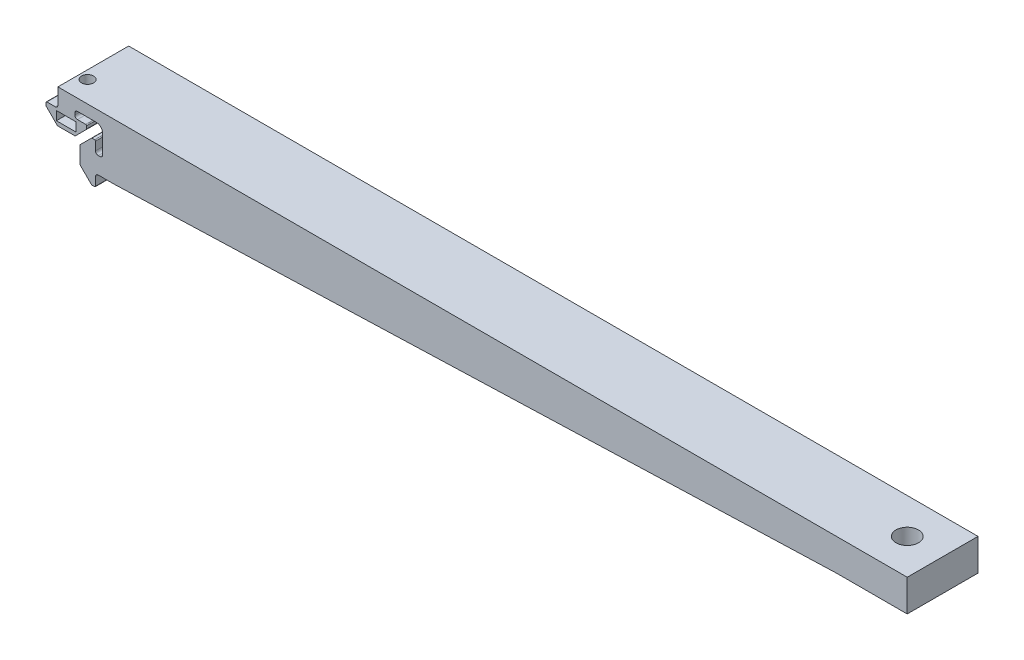
SolidWorks part; units mm, degrees
ref_plane "Front Plane" through (0, 0, 0) normal (0, 0, 1) x (1, 0, 0)
ref_plane "Top Plane" through (0, 0, 0) normal (0, 1, 0) x (1, 0, 0)
ref_plane "Right Plane" through (0, 0, 0) normal (1, 0, 0) x (0, 0, -1)
sketch "Sketch1" plane through (0, 0, 0) normal (0, 0, 1) x (1, 0, 0)
  line L0 (-3.138, 10.25) -> (-8.5, 10.25) construction
  line L1 (-10.25, 8.5) -> (-10.25, 3.138) construction
  line L2 (-9.492, 2.38) -> (-9.008, 2.38) construction
  line L3 (-8.25, 3.138) -> (-8.25, 5.487) construction
  line L4 (-7.992, 5.745) -> (-7.2662, 5.745) construction
  line L5 (-7.0838, 5.6694) -> (-3.9806, 2.5662) construction
  line L6 (-3.905, 2.3838) -> (-3.905, -2.3841) construction
  line L7 (-3.9806, -2.5665) -> (-7.0835, -5.6694) construction
  line L8 (-7.2659, -5.745) -> (-7.992, -5.745) construction
  line L9 (-8.25, -5.487) -> (-8.25, -3.138) construction
  line L10 (-9.008, -2.38) -> (-9.492, -2.38) construction
  line L11 (-10.25, -3.138) -> (-10.25, -8.5) construction
  line L12 (-8.5, -10.25) -> (-3.138, -10.25) construction
  line L13 (-2.38, -9.492) -> (-2.38, -9.008) construction
  line L14 (-3.138, -8.25) -> (-5.487, -8.25) construction
  line L15 (-5.745, -7.992) -> (-5.745, -7.2662) construction
  line L16 (-5.6694, -7.0838) -> (-2.5662, -3.9806) construction
  line L17 (-2.3838, -3.905) -> (2.3841, -3.905) construction
  line L18 (2.5665, -3.9806) -> (5.6694, -7.0835) construction
  line L19 (5.745, -7.2659) -> (5.745, -7.992) construction
  line L20 (5.487, -8.25) -> (3.138, -8.25) construction
  line L21 (2.38, -9.008) -> (2.38, -9.492) construction
  line L22 (3.138, -10.25) -> (8.5, -10.25) construction
  line L23 (10.25, -8.5) -> (10.25, -3.138) construction
  line L24 (9.492, -2.38) -> (9.008, -2.38)
  line L25 (8.25, -3.138) -> (8.25, -5.487)
  line L26 (7.992, -5.745) -> (7.2662, -5.745)
  line L27 (7.0838, -5.6694) -> (3.9806, -2.5662)
  line L28 (3.905, -2.3838) -> (3.905, 2.3841)
  line L29 (3.9806, 2.5665) -> (7.0835, 5.6694)
  line L30 (7.2659, 5.745) -> (7.992, 5.745)
  line L31 (8.25, 5.487) -> (8.25, 3.138)
  line L32 (9.008, 2.38) -> (9.492, 2.38)
  line L33 (10.25, 3.138) -> (10.25, 8.5)
  line L34 (8.5, 10.25) -> (3.138, 10.25)
  line L35 (2.38, 9.492) -> (2.38, 9.008)
  line L36 (3.138, 8.25) -> (5.487, 8.25)
  line L37 (5.745, 7.992) -> (5.745, 7.2662)
  line L38 (5.6694, 7.0838) -> (2.5662, 3.9806)
  line L39 (2.3838, 3.905) -> (-2.3841, 3.905)
  line L40 (-2.5665, 3.9806) -> (-5.6694, 7.0835)
  line L41 (-5.745, 7.2659) -> (-5.745, 7.992)
  line L42 (-5.487, 8.25) -> (-3.138, 8.25)
  line L43 (-2.38, 9.008) -> (-2.38, 9.492)
  line L44 (-10, -3.138) -> (-10, -8.5)
  line L45 (-8.5, -10) -> (-3.138, -10)
  line L46 (-2.63, -9.492) -> (-2.63, -9.008)
  line L47 (-3.138, -8.5) -> (-5.487, -8.5)
  line L48 (-5.995, -7.992) -> (-5.995, -7.2662)
  line L49 (-5.8462, -6.907) -> (-2.743, -3.8038)
  line L50 (-2.3838, -3.655) -> (2.3841, -3.655)
  line L51 (2.7433, -3.8038) -> (5.8462, -6.9067)
  line L52 (5.995, -7.2659) -> (5.995, -7.992)
  line L53 (5.487, -8.5) -> (3.138, -8.5)
  line L54 (2.63, -9.008) -> (2.63, -9.492)
  line L55 (3.138, -10) -> (8.5, -10)
  line L56 (10, -8.5) -> (10, -3.138)
  line L57 (9.492, -2.63) -> (9.008, -2.63)
  line L58 (8.5, -3.138) -> (8.5, -5.487)
  line L59 (7.992, -5.995) -> (7.2662, -5.995)
  line L60 (6.907, -5.8462) -> (3.8038, -2.743)
  line L61 (3.655, -2.3838) -> (3.655, 2.3841)
  line L62 (3.8038, 2.7433) -> (6.9067, 5.8462)
  line L63 (7.2659, 5.995) -> (7.992, 5.995)
  line L64 (8.5, 5.487) -> (8.5, 3.138)
  line L65 (9.008, 2.63) -> (9.492, 2.63)
  line L66 (10, 3.138) -> (10, 8.5)
  line L67 (8.5, 10) -> (3.138, 10)
  line L68 (2.63, 9.492) -> (2.63, 9.008)
  line L69 (3.138, 8.5) -> (5.487, 8.5)
  line L70 (5.995, 7.992) -> (5.995, 7.2662)
  line L71 (5.8462, 6.907) -> (2.743, 3.8038)
  line L72 (2.3838, 3.655) -> (-2.3841, 3.655)
  line L73 (-2.7433, 3.8038) -> (-5.8462, 6.9067)
  line L74 (-5.995, 7.2659) -> (-5.995, 7.992)
  line L75 (-5.487, 8.5) -> (-3.138, 8.5)
  line L76 (-2.63, 9.008) -> (-2.63, 9.492)
  line L77 (-3.138, 10) -> (-8.5, 10)
  line L78 (-10, 8.5) -> (-10, 3.138)
  line L79 (-9.492, 2.63) -> (-9.008, 2.63)
  line L80 (-8.5, 3.138) -> (-8.5, 5.487)
  line L81 (-7.992, 5.995) -> (-7.2662, 5.995)
  line L82 (-6.907, 5.8462) -> (-3.8038, 2.743)
  line L83 (-3.655, 2.3838) -> (-3.655, -2.3841)
  line L84 (-3.8038, -2.7433) -> (-6.9067, -5.8462)
  line L85 (-7.2659, -5.995) -> (-7.992, -5.995)
  line L86 (-8.5, -5.487) -> (-8.5, -3.138)
  line L87 (-9.008, -2.63) -> (-9.492, -2.63)
  line L88 (-10, -3.138) -> (-10, -8.5) construction
  line L89 (-8.5, -10) -> (-3.138, -10) construction
  line L90 (-2.63, -9.492) -> (-2.63, -9.008) construction
  line L91 (-3.138, -8.5) -> (-5.487, -8.5) construction
  line L92 (-5.995, -7.992) -> (-5.995, -7.2662) construction
  line L93 (-5.8462, -6.907) -> (-2.743, -3.8038) construction
  line L94 (-2.3838, -3.655) -> (2.3841, -3.655) construction
  line L95 (2.7433, -3.8038) -> (5.8462, -6.9067) construction
  line L96 (5.995, -7.2659) -> (5.995, -7.992) construction
  line L97 (5.487, -8.5) -> (3.138, -8.5) construction
  line L98 (2.63, -9.008) -> (2.63, -9.492) construction
  line L99 (3.138, -10) -> (8.5, -10) construction
  line L100 (10, -8.5) -> (10, -3.138) construction
  line L101 (9.492, -2.63) -> (9.008, -2.63) construction
  line L102 (8.5, -3.138) -> (8.5, -5.487) construction
  line L103 (7.992, -5.995) -> (7.2662, -5.995) construction
  line L104 (6.907, -5.8462) -> (3.8038, -2.743) construction
  line L105 (3.655, -2.3838) -> (3.655, 2.3841) construction
  line L106 (3.8038, 2.7433) -> (6.9067, 5.8462) construction
  line L107 (7.2659, 5.995) -> (7.992, 5.995) construction
  line L108 (8.5, 5.487) -> (8.5, 3.138) construction
  line L109 (9.008, 2.63) -> (9.492, 2.63) construction
  line L110 (10, 3.138) -> (10, 8.5) construction
  line L111 (8.5, 10) -> (3.138, 10) construction
  line L112 (2.63, 9.492) -> (2.63, 9.008) construction
  line L113 (3.138, 8.5) -> (5.487, 8.5) construction
  line L114 (5.995, 7.992) -> (5.995, 7.2662) construction
  line L115 (5.8462, 6.907) -> (2.743, 3.8038) construction
  line L116 (2.3838, 3.655) -> (-2.3841, 3.655) construction
  line L117 (-2.7433, 3.8038) -> (-5.8462, 6.9067) construction
  line L118 (-5.995, 7.2659) -> (-5.995, 7.992) construction
  line L119 (-5.487, 8.5) -> (-3.138, 8.5) construction
  line L120 (-2.63, 9.008) -> (-2.63, 9.492) construction
  line L121 (-3.138, 10) -> (-8.5, 10) construction
  line L122 (-10, 8.5) -> (-10, 3.138) construction
  line L123 (-9.492, 2.63) -> (-9.008, 2.63) construction
  line L124 (-8.5, 3.138) -> (-8.5, 5.487) construction
  line L125 (-7.992, 5.995) -> (-7.2662, 5.995) construction
  line L126 (-6.907, 5.8462) -> (-3.8038, 2.743) construction
  line L127 (-3.655, 2.3838) -> (-3.655, -2.3841) construction
  line L128 (-3.8038, -2.7433) -> (-6.9067, -5.8462) construction
  line L129 (-7.2659, -5.995) -> (-7.992, -5.995) construction
  line L130 (-8.5, -5.487) -> (-8.5, -3.138) construction
  line L131 (-9.008, -2.63) -> (-9.492, -2.63) construction
  line L132 (-2.38, 9.492) -> (-2.38, 13.492)
  line L133 (-2.38, 13.492) -> (13.492, 13.492)
  line L134 (13.492, 13.492) -> (13.492, -2.38)
  line L135 (13.492, -2.38) -> (9.492, -2.38)
  arc A0 (-8.5, 10.25) -> (-10.25, 8.5) centre (-8.5, 8.5) ccw construction
  arc A1 (-10.25, 3.138) -> (-9.492, 2.38) centre (-9.492, 3.138) ccw construction
  arc A2 (-9.008, 2.38) -> (-8.25, 3.138) centre (-9.008, 3.138) ccw construction
  arc A3 (-7.992, 5.745) -> (-8.25, 5.487) centre (-7.992, 5.487) ccw construction
  arc A4 (-7.0838, 5.6694) -> (-7.2662, 5.745) centre (-7.2662, 5.487) ccw
  arc A5 (-3.905, 2.3838) -> (-3.9806, 2.5662) centre (-4.163, 2.3838) ccw construction
  arc A6 (-3.9806, -2.5665) -> (-3.905, -2.3841) centre (-4.163, -2.3841) ccw construction
  arc A7 (-7.2659, -5.745) -> (-7.0835, -5.6694) centre (-7.2659, -5.487) ccw construction
  arc A8 (-8.25, -5.487) -> (-7.992, -5.745) centre (-7.992, -5.487) ccw construction
  arc A9 (-8.25, -3.138) -> (-9.008, -2.38) centre (-9.008, -3.138) ccw construction
  arc A10 (-9.492, -2.38) -> (-10.25, -3.138) centre (-9.492, -3.138) ccw construction
  arc A11 (-10.25, -8.5) -> (-8.5, -10.25) centre (-8.5, -8.5) ccw construction
  arc A12 (-3.138, -10.25) -> (-2.38, -9.492) centre (-3.138, -9.492) ccw construction
  arc A13 (-2.38, -9.008) -> (-3.138, -8.25) centre (-3.138, -9.008) ccw construction
  arc A14 (-5.745, -7.992) -> (-5.487, -8.25) centre (-5.487, -7.992) ccw
  arc A15 (-5.6694, -7.0838) -> (-5.745, -7.2662) centre (-5.487, -7.2662) ccw construction
  arc A16 (-2.3838, -3.905) -> (-2.5662, -3.9806) centre (-2.3838, -4.163) ccw construction
  arc A17 (2.5665, -3.9806) -> (2.3841, -3.905) centre (2.3841, -4.163) ccw construction
  arc A18 (5.745, -7.2659) -> (5.6694, -7.0835) centre (5.487, -7.2659) ccw construction
  arc A19 (5.487, -8.25) -> (5.745, -7.992) centre (5.487, -7.992) ccw
  arc A20 (3.138, -8.25) -> (2.38, -9.008) centre (3.138, -9.008) ccw construction
  arc A21 (2.38, -9.492) -> (3.138, -10.25) centre (3.138, -9.492) ccw construction
  arc A22 (8.5, -10.25) -> (10.25, -8.5) centre (8.5, -8.5) ccw construction
  arc A23 (10.25, -3.138) -> (9.492, -2.38) centre (9.492, -3.138) ccw construction
  arc A24 (9.008, -2.38) -> (8.25, -3.138) centre (9.008, -3.138) ccw
  arc A25 (7.992, -5.745) -> (8.25, -5.487) centre (7.992, -5.487) ccw
  arc A26 (7.0838, -5.6694) -> (7.2662, -5.745) centre (7.2662, -5.487) ccw
  arc A27 (3.905, -2.3838) -> (3.9806, -2.5662) centre (4.163, -2.3838) ccw
  arc A28 (3.9806, 2.5665) -> (3.905, 2.3841) centre (4.163, 2.3841) ccw
  arc A29 (7.2659, 5.745) -> (7.0835, 5.6694) centre (7.2659, 5.487) ccw
  arc A30 (8.25, 5.487) -> (7.992, 5.745) centre (7.992, 5.487) ccw
  arc A31 (8.25, 3.138) -> (9.008, 2.38) centre (9.008, 3.138) ccw
  arc A32 (9.492, 2.38) -> (10.25, 3.138) centre (9.492, 3.138) ccw
  arc A33 (10.25, 8.5) -> (8.5, 10.25) centre (8.5, 8.5) ccw
  arc A34 (3.138, 10.25) -> (2.38, 9.492) centre (3.138, 9.492) ccw
  arc A35 (2.38, 9.008) -> (3.138, 8.25) centre (3.138, 9.008) ccw
  arc A36 (5.745, 7.992) -> (5.487, 8.25) centre (5.487, 7.992) ccw
  arc A37 (5.6694, 7.0838) -> (5.745, 7.2662) centre (5.487, 7.2662) ccw
  arc A38 (2.3838, 3.905) -> (2.5662, 3.9806) centre (2.3838, 4.163) ccw
  arc A39 (-2.5665, 3.9806) -> (-2.3841, 3.905) centre (-2.3841, 4.163) ccw
  arc A40 (-5.745, 7.2659) -> (-5.6694, 7.0835) centre (-5.487, 7.2659) ccw
  arc A41 (-5.487, 8.25) -> (-5.745, 7.992) centre (-5.487, 7.992) ccw
  arc A42 (-3.138, 8.25) -> (-2.38, 9.008) centre (-3.138, 9.008) ccw
  arc A43 (-2.38, 9.492) -> (-3.138, 10.25) centre (-3.138, 9.492) ccw construction
  arc A44 (-10, -8.5) -> (-8.5, -10) centre (-8.5, -8.5) ccw
  arc A45 (-3.138, -10) -> (-2.63, -9.492) centre (-3.138, -9.492) ccw
  arc A46 (-2.63, -9.008) -> (-3.138, -8.5) centre (-3.138, -9.008) ccw
  arc A47 (-5.995, -7.992) -> (-5.487, -8.5) centre (-5.487, -7.992) ccw
  arc A48 (-5.8462, -6.907) -> (-5.995, -7.2662) centre (-5.487, -7.2662) ccw
  arc A49 (-2.3838, -3.655) -> (-2.743, -3.8038) centre (-2.3838, -4.163) ccw
  arc A50 (2.7433, -3.8038) -> (2.3841, -3.655) centre (2.3841, -4.163) ccw
  arc A51 (5.995, -7.2659) -> (5.8462, -6.9067) centre (5.487, -7.2659) ccw
  arc A52 (5.487, -8.5) -> (5.995, -7.992) centre (5.487, -7.992) ccw
  arc A53 (3.138, -8.5) -> (2.63, -9.008) centre (3.138, -9.008) ccw
  arc A54 (2.63, -9.492) -> (3.138, -10) centre (3.138, -9.492) ccw
  arc A55 (8.5, -10) -> (10, -8.5) centre (8.5, -8.5) ccw
  arc A56 (10, -3.138) -> (9.492, -2.63) centre (9.492, -3.138) ccw
  arc A57 (9.008, -2.63) -> (8.5, -3.138) centre (9.008, -3.138) ccw
  arc A58 (7.992, -5.995) -> (8.5, -5.487) centre (7.992, -5.487) ccw
  arc A59 (6.907, -5.8462) -> (7.2662, -5.995) centre (7.2662, -5.487) ccw
  arc A60 (3.655, -2.3838) -> (3.8038, -2.743) centre (4.163, -2.3838) ccw
  arc A61 (3.8038, 2.7433) -> (3.655, 2.3841) centre (4.163, 2.3841) ccw
  arc A62 (7.2659, 5.995) -> (6.9067, 5.8462) centre (7.2659, 5.487) ccw
  arc A63 (8.5, 5.487) -> (7.992, 5.995) centre (7.992, 5.487) ccw
  arc A64 (8.5, 3.138) -> (9.008, 2.63) centre (9.008, 3.138) ccw
  arc A65 (9.492, 2.63) -> (10, 3.138) centre (9.492, 3.138) ccw
  arc A66 (10, 8.5) -> (8.5, 10) centre (8.5, 8.5) ccw
  arc A67 (3.138, 10) -> (2.63, 9.492) centre (3.138, 9.492) ccw
  arc A68 (2.63, 9.008) -> (3.138, 8.5) centre (3.138, 9.008) ccw
  arc A69 (5.995, 7.992) -> (5.487, 8.5) centre (5.487, 7.992) ccw
  arc A70 (5.8462, 6.907) -> (5.995, 7.2662) centre (5.487, 7.2662) ccw
  arc A71 (2.3838, 3.655) -> (2.743, 3.8038) centre (2.3838, 4.163) ccw
  arc A72 (-2.7433, 3.8038) -> (-2.3841, 3.655) centre (-2.3841, 4.163) ccw
  arc A73 (-5.995, 7.2659) -> (-5.8462, 6.9067) centre (-5.487, 7.2659) ccw
  arc A74 (-5.487, 8.5) -> (-5.995, 7.992) centre (-5.487, 7.992) ccw
  arc A75 (-3.138, 8.5) -> (-2.63, 9.008) centre (-3.138, 9.008) ccw
  arc A76 (-2.63, 9.492) -> (-3.138, 10) centre (-3.138, 9.492) ccw
  arc A77 (-8.5, 10) -> (-10, 8.5) centre (-8.5, 8.5) ccw
  arc A78 (-10, 3.138) -> (-9.492, 2.63) centre (-9.492, 3.138) ccw
  arc A79 (-9.008, 2.63) -> (-8.5, 3.138) centre (-9.008, 3.138) ccw
  arc A80 (-7.992, 5.995) -> (-8.5, 5.487) centre (-7.992, 5.487) ccw
  arc A81 (-6.907, 5.8462) -> (-7.2662, 5.995) centre (-7.2662, 5.487) ccw
  arc A82 (-3.655, 2.3838) -> (-3.8038, 2.743) centre (-4.163, 2.3838) ccw
  arc A83 (-3.8038, -2.7433) -> (-3.655, -2.3841) centre (-4.163, -2.3841) ccw
  arc A84 (-7.2659, -5.995) -> (-6.9067, -5.8462) centre (-7.2659, -5.487) ccw
  arc A85 (-8.5, -5.487) -> (-7.992, -5.995) centre (-7.992, -5.487) ccw
  arc A86 (-8.5, -3.138) -> (-9.008, -2.63) centre (-9.008, -3.138) ccw
  arc A87 (-9.492, -2.63) -> (-10, -3.138) centre (-9.492, -3.138) ccw
  arc A88 (-10, -8.5) -> (-8.5, -10) centre (-8.5, -8.5) ccw construction
  arc A89 (-3.138, -10) -> (-2.63, -9.492) centre (-3.138, -9.492) ccw construction
  arc A90 (-2.63, -9.008) -> (-3.138, -8.5) centre (-3.138, -9.008) ccw construction
  arc A91 (-5.995, -7.992) -> (-5.487, -8.5) centre (-5.487, -7.992) ccw construction
  arc A92 (-5.8462, -6.907) -> (-5.995, -7.2662) centre (-5.487, -7.2662) ccw construction
  arc A93 (-2.3838, -3.655) -> (-2.743, -3.8038) centre (-2.3838, -4.163) ccw construction
  arc A94 (2.7433, -3.8038) -> (2.3841, -3.655) centre (2.3841, -4.163) ccw construction
  arc A95 (5.995, -7.2659) -> (5.8462, -6.9067) centre (5.487, -7.2659) ccw construction
  arc A96 (5.487, -8.5) -> (5.995, -7.992) centre (5.487, -7.992) ccw construction
  arc A97 (3.138, -8.5) -> (2.63, -9.008) centre (3.138, -9.008) ccw construction
  arc A98 (2.63, -9.492) -> (3.138, -10) centre (3.138, -9.492) ccw construction
  arc A99 (8.5, -10) -> (10, -8.5) centre (8.5, -8.5) ccw construction
  arc A100 (10, -3.138) -> (9.492, -2.63) centre (9.492, -3.138) ccw construction
  arc A101 (9.008, -2.63) -> (8.5, -3.138) centre (9.008, -3.138) ccw construction
  arc A102 (7.992, -5.995) -> (8.5, -5.487) centre (7.992, -5.487) ccw construction
  arc A103 (6.907, -5.8462) -> (7.2662, -5.995) centre (7.2662, -5.487) ccw construction
  arc A104 (3.655, -2.3838) -> (3.8038, -2.743) centre (4.163, -2.3838) ccw construction
  arc A105 (3.8038, 2.7433) -> (3.655, 2.3841) centre (4.163, 2.3841) ccw construction
  arc A106 (7.2659, 5.995) -> (6.9067, 5.8462) centre (7.2659, 5.487) ccw construction
  arc A107 (8.5, 5.487) -> (7.992, 5.995) centre (7.992, 5.487) ccw construction
  arc A108 (8.5, 3.138) -> (9.008, 2.63) centre (9.008, 3.138) ccw construction
  arc A109 (9.492, 2.63) -> (10, 3.138) centre (9.492, 3.138) ccw construction
  arc A110 (10, 8.5) -> (8.5, 10) centre (8.5, 8.5) ccw construction
  arc A111 (3.138, 10) -> (2.63, 9.492) centre (3.138, 9.492) ccw construction
  arc A112 (2.63, 9.008) -> (3.138, 8.5) centre (3.138, 9.008) ccw construction
  arc A113 (5.995, 7.992) -> (5.487, 8.5) centre (5.487, 7.992) ccw construction
  arc A114 (5.8462, 6.907) -> (5.995, 7.2662) centre (5.487, 7.2662) ccw construction
  arc A115 (2.3838, 3.655) -> (2.743, 3.8038) centre (2.3838, 4.163) ccw construction
  arc A116 (-2.7433, 3.8038) -> (-2.3841, 3.655) centre (-2.3841, 4.163) ccw construction
  arc A117 (-5.995, 7.2659) -> (-5.8462, 6.9067) centre (-5.487, 7.2659) ccw construction
  arc A118 (-5.487, 8.5) -> (-5.995, 7.992) centre (-5.487, 7.992) ccw construction
  arc A119 (-3.138, 8.5) -> (-2.63, 9.008) centre (-3.138, 9.008) ccw construction
  arc A120 (-2.63, 9.492) -> (-3.138, 10) centre (-3.138, 9.492) ccw construction
  arc A121 (-8.5, 10) -> (-10, 8.5) centre (-8.5, 8.5) ccw construction
  arc A122 (-10, 3.138) -> (-9.492, 2.63) centre (-9.492, 3.138) ccw construction
  arc A123 (-9.008, 2.63) -> (-8.5, 3.138) centre (-9.008, 3.138) ccw construction
  arc A124 (-7.992, 5.995) -> (-8.5, 5.487) centre (-7.992, 5.487) ccw construction
  arc A125 (-6.907, 5.8462) -> (-7.2662, 5.995) centre (-7.2662, 5.487) ccw construction
  arc A126 (-3.655, 2.3838) -> (-3.8038, 2.743) centre (-4.163, 2.3838) ccw construction
  arc A127 (-3.8038, -2.7433) -> (-3.655, -2.3841) centre (-4.163, -2.3841) ccw construction
  arc A128 (-7.2659, -5.995) -> (-6.9067, -5.8462) centre (-7.2659, -5.487) ccw construction
  arc A129 (-8.5, -5.487) -> (-7.992, -5.995) centre (-7.992, -5.487) ccw construction
  arc A130 (-8.5, -3.138) -> (-9.008, -2.63) centre (-9.008, -3.138) ccw construction
  arc A131 (-9.492, -2.63) -> (-10, -3.138) centre (-9.492, -3.138) ccw construction
  dimension "D3" = 4
  dimension "D4" = 4
  dimension "D1" = 0
  dimension "D2" = 0.25
extrude "Boss-Extrude1" add sketch "Sketch1" against normal blind 20 contours A42 L42 A41 L41 A40 L40 A39 L39 A38 L38 A37 L37 A36 L36 A35 L35 A34 L34 A33 L33 A32 L32 A31 L31 A30 L30 A29 L29 A28 L28 A27 L27 A26 L26 A25 L25 A24 L24 L135 L134 L133 L132 L43
sketch "Sketch2" plane through (0, 0, 0) normal (0, 0, 1) x (1, 0, 0)
  line L0 (13.492, 13.492) -> (237.62, 13.492)
  line L1 (237.62, 13.492) -> (237.62, 9.492)
  line L2 (237.62, 9.492) -> (13.492, -2.38)
  line L3 (-2.38, 9.008) -> (-2.38, 13.492) construction
  line L4 (13.492, -2.38) -> (13.492, 13.492)
  dimension "D1" = 4
  dimension "D2" = 240
extrude "Boss-Extrude2" add sketch "Sketch2" against normal up to surface (20 mm away) up to face at (4.3948, 4.3949, -20)
sketch "Sketch3" plane through (0, 0, 0) normal (0, 0, 1) x (1, 0, 0)
  line L0 (-2.38, 13.492) -> (237.62, 13.492) construction
  line L1 (237.62, 9.492) -> (217.62, 9.492)
  line L2 (237.62, 9.492) -> (237.62, 13.492) construction
  line L3 (237.62, 13.492) -> (217.62, 13.492) construction
  line L4 (217.62, 9.492) -> (217.62, 13.492) construction
  line L5 (217.62, 9.492) -> (217.62, 8.4326)
  line L6 (13.492, -2.38) -> (237.62, 9.492) construction
  line L7 (217.62, 8.4326) -> (237.62, 9.492)
  dimension "D1" = 20
extrude "Cut-Extrude1" cut sketch "Sketch3" against normal up to surface (20 mm away) contours L1 L5 L7 up to face at (15.2842, 4.5162, -20)
sketch "Sketch4" plane through (0, 9.492, 0) normal (0, -1, 0) x (1, 0, 0)
  line L0 (217.62, -10) -> (237.62, -10) construction
  line L1 (217.62, -20) -> (217.62, 0) construction
  line L2 (237.62, -20) -> (237.62, 0) construction
  circle A0 centre (227.62, -10) radius 3.175
  dimension "D1" = 6.35
extrude "Cut-Extrude2" cut sketch "Sketch4" against normal up to surface (4 mm away) up to face at (117.62, 13.492, -10)
sketch "Sketch5" plane through (0, 9.492, 0) normal (0, -1, 0) x (1, 0, 0)
  line L4 (217.62, -20) -> (237.62, -20)
  line L5 (237.62, -20) -> (237.62, 0)
  line L6 (237.62, 0) -> (217.62, 0)
  line L7 (217.62, 0) -> (217.62, -20)
  line L8 (217.62, -20) -> (237.62, -20)
  line L9 (237.62, -20) -> (237.62, 0)
  line L10 (237.62, 0) -> (217.62, 0)
  line L11 (217.62, 0) -> (217.62, -20)
  circle A0 centre (227.62, -10) radius 3.175 construction
  circle A1 centre (227.62, -10) radius 3.175
  dimension "D1" = 0
extrude "Boss-Extrude3" add sketch "Sketch5" along normal blind 5 contours A1 | L10 L11 L8 L9
sketch "Sketch6" plane through (0, 0, 0) normal (0, 0, 1) x (1, 0, 0)
  line L0 (13.492, -2.38) -> (217.62, 4.492)
  line L1 (217.62, 4.492) -> (217.62, 8.4326)
  line L2 (217.62, 8.4326) -> (13.492, -2.38)
extrude "Boss-Extrude4" add sketch "Sketch6" against normal up to surface (20 mm away) up to face at (24.4813, 4.491, -20)
sketch "Sketch7" plane through (0, 0, 0) normal (0, 0, 1) x (1, 0, 0)
  line L1 (-1.772, 6.7024) -> (1.9234, 6.7024)
  line L2 (-1.772, 6.7024) -> (-1.772, 5.3816)
  line L3 (-1.772, 5.3816) -> (1.9234, 5.3816)
  line L4 (1.9234, 6.7024) -> (1.9234, 5.3816)
sketch "Sketch8" plane through (0, 13.492, 0) normal (0, 1, 0) x (1, 0, 0)
  line L0 (2.3838, 0) -> (-2.3841, 0) construction
  line L1 (2.3838, 0) -> (-2.3841, 0)
  line L2 (-0.0002, 2.7668) -> (-0.0002, 6) construction
  line L3 (-2.8002, 4.3834) -> (-2.8002, 0)
  line L4 (2.7998, 4.3834) -> (2.7998, 7.6166)
  line L5 (2.7998, 7.6166) -> (-0.0002, 9.2332)
  line L6 (-0.0002, 9.2332) -> (-2.8002, 7.6166)
  line L7 (-2.8002, 7.6166) -> (-2.8002, 4.3834)
  line L8 (-1.4002, 3.5751) -> (-0.0002, 2.7668) construction
  line L9 (1.3998, 3.5751) -> (2.7998, 4.3834) construction
  line L10 (-2.8002, 0) -> (-2.3841, 0)
  line L11 (2.7998, 4.3834) -> (2.7998, 0)
  line L12 (-2.38, 0) -> (237.62, 0) construction
  line L13 (2.7998, 0) -> (2.3838, 0)
  line L14 (-2.8002, 4.3834) -> (-1.4002, 3.5751) construction
  line L15 (-0.0002, 0) -> (-0.0002, 2.7668) construction
  line L16 (-0.0002, 2.7668) -> (1.3998, 3.5751) construction
  arc A0 (2.7998, 6) -> (-2.8002, 6) centre (-0.0002, 6) ccw construction
  arc A1 (-2.8002, 6) -> (-1.4002, 3.5751) centre (-0.0002, 6) ccw construction
  arc A2 (-1.4002, 3.5751) -> (-0.0002, 3.2) centre (-0.0002, 6) ccw construction
  arc A3 (-0.0002, 3.2) -> (1.3998, 3.5751) centre (-0.0002, 6) ccw construction
  arc A4 (1.3998, 3.5751) -> (2.7998, 6) centre (-0.0002, 6) ccw construction
  dimension "D1" = 5.6
  dimension "D2" = 6
extrude "Cut-Extrude3" cut sketch "Sketch8" against normal blind 2.5 from offset 6 contours L3 L10 L1 L13 L11 L4 L5 L6 L7 offset against normal yes
sketch "Sketch9" plane through (0, 13.492, 0) normal (0, 1, 0) x (1, 0, 0)
  line L0 (2.7998, 7.6166) -> (-0.0002, 9.2332) construction
  line L1 (-0.0002, 9.2332) -> (-2.8002, 7.6166) construction
  line L2 (2.7998, 7.6166) -> (1.3998, 8.4249) construction
  line L3 (-0.0002, 9.2332) -> (-1.4002, 8.4249) construction
  line L4 (-2.8002, 7.6166) -> (-2.8002, 6) construction
  line L5 (2.7998, 7.6166) -> (1.3998, 8.4249) construction
  line L6 (-0.0002, 9.2332) -> (-1.4002, 8.4249) construction
  line L7 (-2.8002, 6) -> (-2.8002, 4.3834) construction
  line L8 (-2.8002, 4.3834) -> (-1.4002, 3.5751) construction
  line L9 (-0.0002, 2.7668) -> (1.3998, 3.5751) construction
  line L10 (2.7998, 4.3834) -> (2.7998, 6) construction
  line L11 (-1.4002, 8.4249) -> (-2.8002, 7.6166) construction
  line L12 (-1.4002, 8.4249) -> (-2.8002, 7.6166) construction
  line L13 (1.3998, 8.4249) -> (-0.0002, 9.2332) construction
  line L14 (1.3998, 8.4249) -> (-0.0002, 9.2332) construction
  line L15 (2.7998, 6) -> (2.7998, 7.6166) construction
  line L16 (1.3998, 3.5751) -> (2.7998, 4.3834) construction
  line L17 (-1.4002, 3.5751) -> (-0.0002, 2.7668) construction
  circle A0 centre (-0.0002, 6) radius 2.8 construction
  circle A1 centre (-0.0002, 6) radius 1.7
  dimension "D1" = 3.4
extrude "Cut-Extrude4" cut sketch "Sketch9" against normal through all
